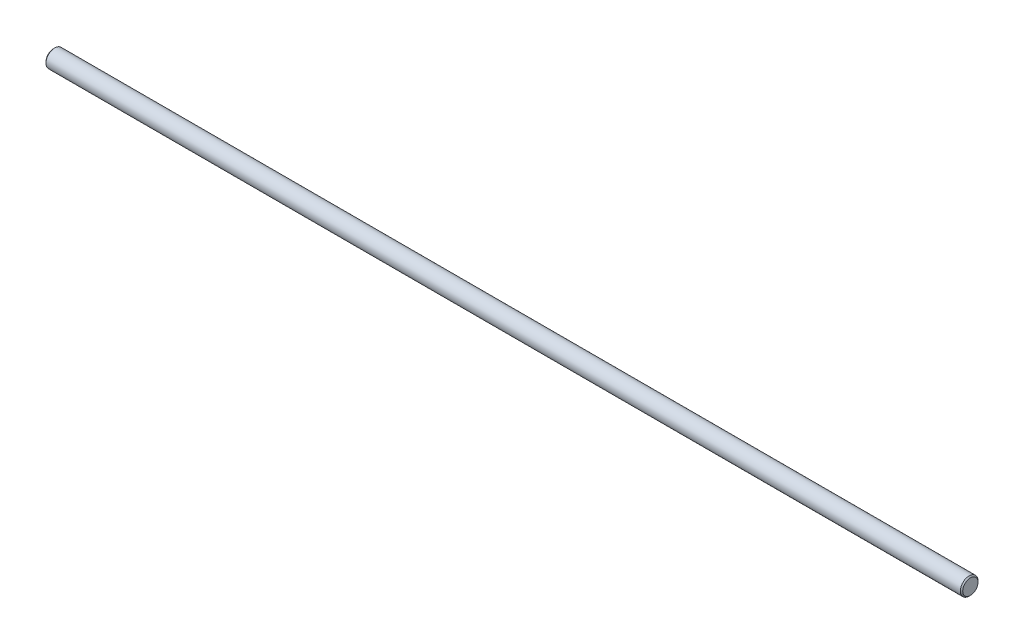
SolidWorks part; units mm, degrees
ref_plane "Plan de face" through (0, 0, 0) normal (0, 0, 1) x (1, 0, 0)
ref_plane "Plan de dessus" through (0, 0, 0) normal (0, 1, 0) x (1, 0, 0)
ref_plane "Plan de droite" through (0, 0, 0) normal (1, 0, 0) x (0, 0, -1)
sketch "Esquisse1" plane through (0, 0, 0) normal (1, 0, 0) x (0, 0, -1)
  circle A0 centre (0, 0) radius 1.5
extrude "Boss.-Extru.1" add sketch "Esquisse1" along normal blind 156
chamfer "Chanfrein1" distance 0.2 angle 45 2 edges at (0, 0, -1.5) (156, 0, -1.5)
